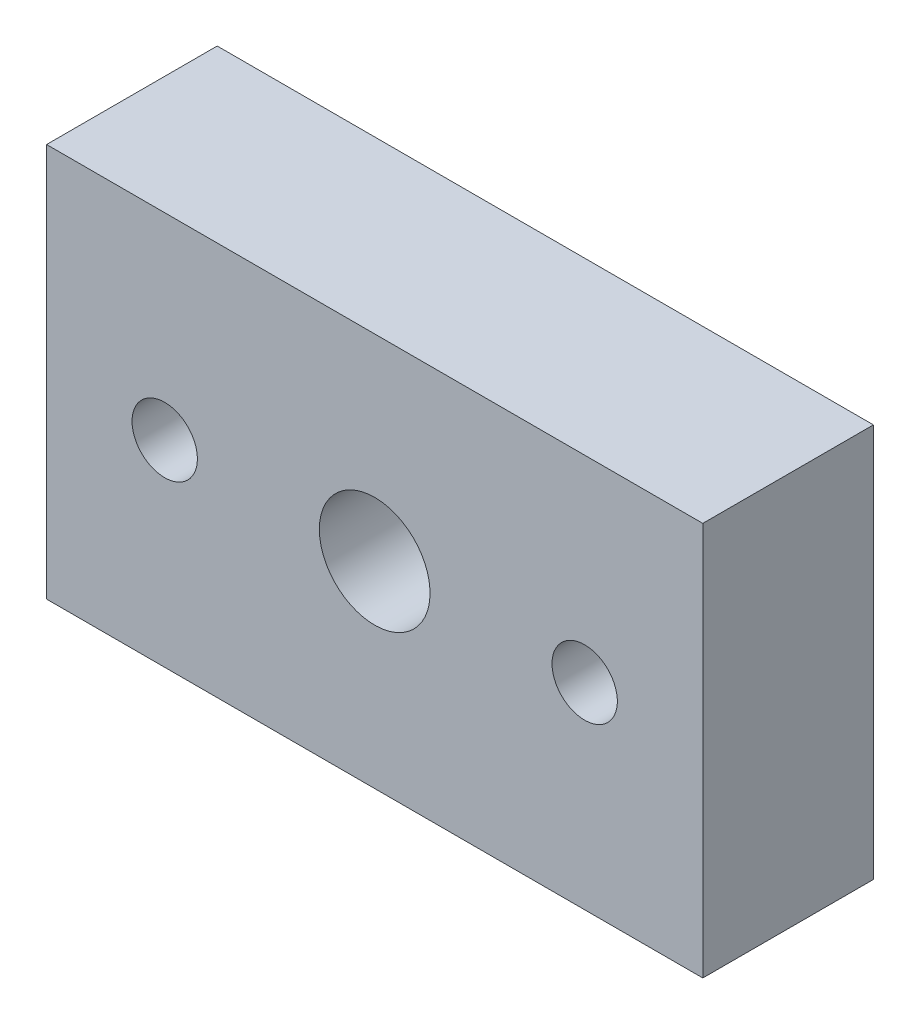
SolidWorks part; units mm, degrees
material "6061-T6 (SS)"
ref_plane "Front Plane" through (0, 0, 0) normal (0, 0, 1) x (1, 0, 0)
ref_plane "Top Plane" through (0, 0, 0) normal (0, 1, 0) x (1, 0, 0)
ref_plane "Right Plane" through (0, 0, 0) normal (1, 0, 0) x (0, 0, -1)
sketch "Sketch1" plane through (0, 0, 0) normal (0, 0, 1) x (1, 0, 0)
  line L1 (-25, -15) -> (25, -15)
  line L2 (-25, -15) -> (-25, 15)
  line L3 (-25, 15) -> (25, 15)
  line L4 (25, -15) -> (25, 15)
  line L5 (-25, -15) -> (25, 15) construction
  line L6 (-25, 15) -> (25, -15) construction
  point P0 (0, 0)
  dimension "D1" = 50
  dimension "D2" = 30
extrude "Boss-Extrude1" add sketch "Sketch1" along normal blind 13
hole_wizard "Tap Drill for 5/16-18 Helicoil1" positions "Sketch3" profile "Sketch2" hole size "5/16-18" standard "ANSI Inch"
sketch "Sketch3" plane through (0, 0, 0) normal (0, 0, -1) x (-1, 0, 0)
  point P0 (0, 0)
sketch "Sketch2" plane through (0, 0, 0) normal (1, 0, 0) x (0, 1, 0)
  line L0 (0, 0) -> (0, 132.0635)
  line L1 (0, 132.0635) -> (4.2164, 129.53)
  line L2 (4.2164, 129.53) -> (4.2164, 0)
  line L5 (4.2164, 0) -> (0, 0)
  line L10 (0, 132.0635) -> (-4.2164, 129.53) construction
  line L11 (0, -6.35) -> (0, 107.95) construction
  dimension "Hole Dia." = 8.4328
  dimension "Hole Depth" = 129.53
  dimension "Drill Angle" = 118
hole_wizard "#10 Clearance Hole1" positions "Sketch5" profile "Sketch4" hole size "#10" standard "ANSI Inch"
sketch "Sketch5" plane through (0, 0, 0) normal (0, 0, -1) x (-1, 0, 0)
  line L0 (0, 0) -> (26.5212, 0) construction
  line L1 (0, 0) -> (0, 24.3716) construction
  point P0 (-16, 0)
  point P10 (16, 0)
  dimension "D1" = 16
sketch "Sketch4" plane through (16, 0, 0) normal (1, 0, 0) x (0, 1, 0)
  line L0 (0, 0) -> (0, 131.0257)
  line L1 (0, 131.0257) -> (2.4892, 129.53)
  line L2 (2.4892, 129.53) -> (2.4892, 0)
  line L5 (2.4892, 0) -> (0, 0)
  line L10 (0, 131.0257) -> (-2.4892, 129.53) construction
  line L11 (0, -6.35) -> (0, 107.95) construction
  dimension "Hole Dia." = 4.9784
  dimension "Hole Depth" = 129.53
  dimension "Drill Angle" = 118
